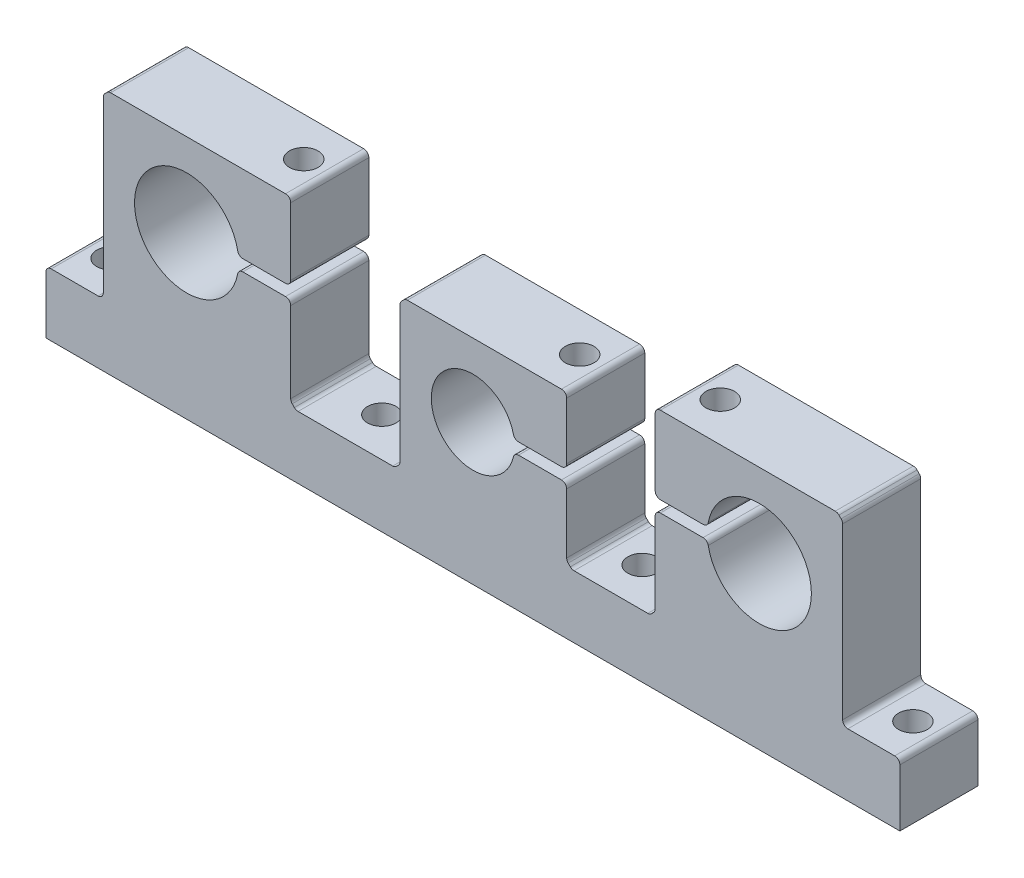
SolidWorks part; units mm, degrees
ref_plane "Front Plane" through (0, 0, 0) normal (0, 0, 1) x (1, 0, 0)
ref_plane "Top Plane" through (0, 0, 0) normal (0, 1, 0) x (1, 0, 0)
ref_plane "Right Plane" through (0, 0, 0) normal (1, 0, 0) x (0, 0, -1)
sketch "Sketch1" plane through (0, 0, 0) normal (0, 0, 1) x (1, 0, 0)
  line L0 (0, 0) -> (0, 57.1903) construction
  line L1 (82, 0) -> (-82, 0)
  line L2 (-82, 0) -> (-82, 12)
  line L3 (-82, 12) -> (-71, 12)
  line L4 (-71, 12) -> (-71, 47)
  line L5 (-71, 47) -> (71, 47)
  line L6 (82, 0) -> (82, 12)
  line L7 (82, 12) -> (71, 12)
  line L8 (71, 12) -> (71, 47)
  point P12 (0, 47)
  dimension "D1" = 82
  dimension "D2" = 12
  dimension "D3" = 47
  dimension "D4" = 71
extrude "Boss-Extrude1" add sketch "Sketch1" along normal blind 15
sketch "Sketch2" plane through (0, 0, 15) normal (0, 0, 1) x (1, 0, 0)
  line L0 (0, 0) -> (0, 27) construction
  line L1 (-82, 0) -> (82, 0) construction
  circle A0 centre (0, 27) radius 8
  dimension "D1" = 16
  dimension "D2" = 27
extrude "Cut-Extrude1" cut sketch "Sketch2" against normal up to next
sketch "Sketch3" plane through (0, 0, 0) normal (0, 0, -1) x (-1, 0, 0)
  line L0 (0, 0) -> (0, 47) construction
  line L1 (-71, 47) -> (71, 47) construction
  line L2 (-71, 31) -> (-55, 31) construction
  line L3 (-71, 12) -> (-71, 47) construction
  line L4 (82, 0) -> (-82, 0) construction
  circle A0 centre (-55, 31) radius 10
  circle A1 centre (55, 31) radius 10
  point P10 (-63, 31)
  dimension "D1" = 20
  dimension "D2" = 31
  dimension "D3" = 16
extrude "Cut-Extrude2" cut sketch "Sketch3" against normal up to next
sketch "Sketch6" plane through (0, 12, 0) normal (0, 1, 0) x (1, 0, 0)
  line L0 (-82, -7.5) -> (82, -7.5) construction
  line L1 (-82, -15) -> (-82, 0) construction
  line L2 (82, -15) -> (82, 0) construction
  line L3 (-82, -2.0107) -> (-77, -2.0107) construction
  line L4 (-77, 0) -> (-77, -9.4844) construction
  line L5 (-71, 0) -> (-82, 0) construction
  line L6 (82, -3.3711) -> (77, -3.3711) construction
  line L7 (77, -3.3711) -> (77, -12.0015) construction
  dimension "D1" = 5
  dimension "D2" = 5
hole_wizard "Ø5.5 (5.5) Diameter Hole1" positions "3DSketch3" profile "Sketch8" hole size "Ø5.5" standard "GB" end condition up to next
sketch3d "3DSketch3"
  line L0 (-82, 12, 7.5) -> (82, 12, 7.5) construction
  line L1 (-77, 12, 0) -> (-77, 12, 9.4844) construction
  line L2 (77, 12, 3.3711) -> (77, 12, 12.0015) construction
  point P0 (-77, 12, 7.5)
  point P6 (77, 12, 7.5)
sketch "Sketch8" plane through (-77, 12, 7.5) normal (1, 0, 0) x (0, 0, 1)
  line L0 (0, 0) -> (0, 12)
  line L1 (0, 12) -> (2.75, 12)
  line L2 (2.75, 12) -> (2.75, 0)
  line L5 (2.75, 0) -> (0, 0)
  line L11 (0, -6.35) -> (0, 107.95) construction
  dimension "Thru Hole Dia." = 5.5
  dimension "Thru Hole Depth" = 12
sketch "Sketch9" plane through (0, 0, 15) normal (0, 0, 1) x (1, 0, 0)
  line L0 (0, 0.821) -> (0, 56.8906) construction
  line L1 (0, 41) -> (-14, 41)
  line L2 (-14, 41) -> (-14, 12)
  line L3 (-14, 12) -> (-35, 12)
  line L4 (-35, 12) -> (-35, 47)
  line L5 (71, 47) -> (-71, 47) construction
  line L6 (0, 41) -> (18, 41)
  line L7 (18, 41) -> (18, 12)
  line L8 (18, 12) -> (35, 12)
  line L9 (35, 12) -> (35, 47)
  line L10 (-82, 0) -> (82, 0) construction
  line L11 (-55, 31) -> (-55, 50.7523) construction
  line L12 (-35, 47) -> (35, 47)
  point P19 (26.5, 12)
  dimension "D1" = 14
  dimension "D2" = 6
  dimension "D3" = 18
  dimension "D4" = 12
  dimension "D5" = 20
  dimension "D6" = 12
  dimension "D7" = 35
extrude "Cut-Extrude3" cut sketch "Sketch9" against normal up to next
sketch "Sketch10" plane through (0, 0, 15) normal (0, 0, 1) x (1, 0, 0)
  line L0 (-55, 31) -> (55, 31) construction
  line L1 (-55, 31) -> (-98.7374, 31) construction
  line L2 (55, 31) -> (79.8304, 31) construction
  line L3 (0, 27) -> (28.6792, 27) construction
  line L4 (-55, 31) -> (-55, 32.1)
  line L5 (-55, 32.1) -> (-35, 32.1)
  line L6 (-35, 47) -> (-35, 12) construction
  line L7 (-55, 31) -> (-55, 29.9)
  line L8 (-55, 29.9) -> (-35, 29.9)
  line L9 (-35, 32.1) -> (-35, 29.9)
  line L10 (55, 31) -> (55, 32.1)
  line L11 (55, 32.1) -> (35, 32.1)
  line L12 (35, 12) -> (35, 47) construction
  line L13 (55, 31) -> (55, 29.9)
  line L14 (55, 29.9) -> (35, 29.9)
  line L15 (35, 32.1) -> (35, 29.9)
  line L16 (0, 27) -> (0, 28.1)
  line L17 (0, 28.1) -> (18, 28.1)
  line L18 (18, 41) -> (18, 12) construction
  line L19 (18, 28.1) -> (18, 25.9)
  line L20 (18, 25.9) -> (0, 25.9)
  line L21 (0, 25.9) -> (0, 27)
  dimension "D1" = 1.1
  dimension "D2" = 1.1
  dimension "D3" = 1.1
  dimension "D4" = 1.1
extrude "Cut-Extrude4" cut sketch "Sketch10" against normal up to next
sketch "Sketch11" plane through (0, 47, 0) normal (0, 1, 0) x (1, 0, 0)
  line L0 (-82, -7.5) -> (82, -7.5) construction
  line L1 (-82, -15) -> (-82, 0) construction
  line L2 (82, -15) -> (82, 0) construction
  line L3 (-40, -1.2511) -> (-40, -12.3189) construction
  line L4 (-35, 0) -> (-35, -15) construction
  line L5 (40, -1.2511) -> (40, -13.334) construction
  line L6 (35, 0) -> (35, -15) construction
  line L7 (13, -2.4134) -> (13, -12.3189) construction
  line L8 (18, 0) -> (18, -15) construction
  dimension "D1" = 5
  dimension "D2" = 5
  dimension "D3" = 5
hole_wizard "Ø5.5 (5.5) Diameter Hole2" positions "3DSketch4" profile "Sketch12" hole size "Ø5.5" standard "GB" end condition up to next
sketch3d "3DSketch4"
  line L0 (-82, 47, 7.5) -> (82, 47, 7.5) construction
  line L1 (-40, 47, 1.2511) -> (-40, 47, 12.3189) construction
  line L2 (40, 47, 1.2511) -> (40, 47, 13.334) construction
  point P0 (-40, 47, 7.5)
  point P6 (40, 47, 7.5)
sketch "Sketch12" plane through (-40, 47, 7.5) normal (1, 0, 0) x (0, 0, 1)
  line L0 (0, 0) -> (0, 14.9)
  line L1 (0, 14.9) -> (2.75, 14.9)
  line L2 (2.75, 14.9) -> (2.75, 0)
  line L5 (2.75, 0) -> (0, 0)
  line L11 (0, -6.35) -> (0, 107.95) construction
  dimension "Thru Hole Dia." = 5.5
  dimension "Thru Hole Depth" = 14.9
hole_wizard "Ø5.5 (5.5) Diameter Hole3" positions "3DSketch6" profile "Sketch14" hole size "Ø5.5" standard "GB"
sketch3d "3DSketch6"
  line L0 (-82, 47, 7.5) -> (82, 47, 7.5) construction
  line L1 (13, 47, 2.4134) -> (13, 47, 12.3189) construction
  line L2 (40, 32.1, 7.5) -> (40, 47, 7.5) construction
  line L3 (-40, 32.1, 7.5) -> (-40, 47, 7.5) construction
  point P0 (13, 47, 7.5)
  point P6 (42.7784, 0, -5.3643)
  point P8 (40, 47, 7.5)
  point P12 (-40, 47, 7.5)
sketch "Sketch14" plane through (13, 47, 7.5) normal (1, 0, 0) x (0, 0, 1)
  line L0 (0, 0) -> (0, 18.9)
  line L1 (0, 18.9) -> (2.75, 18.9)
  line L2 (2.75, 18.9) -> (2.75, 0)
  line L5 (2.75, 0) -> (0, 0)
  line L11 (0, -6.35) -> (0, 107.95) construction
  dimension "Thru Hole Dia." = 5.5
  dimension "Thru Hole Depth" = 18.9
sketch "Sketch16" plane through (0, 29.9, 0) normal (0, 1, 0) x (1, 0, 0)
  line L0 (-40, -7.5) -> (40, -7.5) construction
hole_wizard "M5 Tapped Hole2" positions "3DSketch9" profile "Sketch18" tap size "M5" standard "GB"
sketch3d "3DSketch9"
  point P0 (-40, 29.9, 7.5)
  point P3 (40, 29.9, 7.5)
sketch "Sketch18" plane through (-40, 29.9, 7.5) normal (1, 0, 0) x (0, 0, 1)
  line L0 (0, 0) -> (0, 15.2618)
  line L1 (0, 15.2618) -> (2.1, 14)
  line L2 (2.1, 14) -> (2.1, 0)
  line L5 (2.1, 0) -> (0, 0)
  line L10 (0, 15.2618) -> (-2.1, 14) construction
  line L11 (0, -6.35) -> (0, 107.95) construction
  dimension "Tap Drill Dia." = 4.2
  dimension "Tap Drill Depth" = 14
  dimension "Drill Angle" = 118
cosmetic thread "Hole Thread1" parameters "D1"=10, "D2"=5
cosmetic thread "Hole Thread2" parameters "D1"=10, "D2"=5
chamfer "Chamfer1" distance 1 angle 45 2 edges at (-71, 47, 7.5) (71, 47, 7.5)
chamfer "Chamfer2" distance 1 angle 45 1 edges at (-14, 41, 7.5)
chamfer "Chamfer3" distance 1 angle 45 4 edges at (35, 12, 7.5) (18, 12, 7.5) (-14, 12, 7.5) (-35, 12, 7.5)
fillet "Fillet1" radius 1 33 edges at (82, 12, 7.5) (71, 12, 7.5) (71, 46, 7.5) (70, 47, 7.5) (45.0607, 29.9, 7.5) (45.0607, 32.1, 7.5) (35, 47, 7.5) (35, 32.1, 7.5) (35, 29.9, 7.5) (35, 13, 7.5) (34, 12, 7.5) (19, 12, 7.5) (18, 13, 7.5) (18, 25.9, 7.5) (7.924, 25.9, 7.5) (7.924, 28.1, 7.5) (18, 28.1, 7.5) (18, 41, 7.5) (-13, 41, 7.5) (-14, 40, 7.5) (-14, 13, 7.5) (-15, 12, 7.5) (-34, 12, 7.5) (-35, 13, 7.5) (-35, 29.9, 7.5) (-45.0607, 29.9, 7.5) (-45.0607, 32.1, 7.5) (-35, 32.1, 7.5) (-35, 47, 7.5) (-70, 47, 7.5) (-71, 46, 7.5) (-71, 12, 7.5) (-82, 12, 7.5)
sketch "Sketch19" plane through (0, 12, 0) normal (0, 1, 0) x (1, 0, 0)
  line L0 (0, 0) -> (0, -46.8367) construction
  line L1 (-40, -7.5) -> (85.486, -7.5) construction
  line L2 (-25, -7.5) -> (-25, -38.4714) construction
  line L3 (25, -7.5) -> (25, -37.1964) construction
  dimension "D1" = 25
  dimension "D2" = 25
hole_wizard "Ø5.5 (5.5) Diameter Hole4" positions "3DSketch10" profile "Sketch20" hole size "Ø5.5" standard "GB" end condition through all
sketch3d "3DSketch10"
  point P0 (-25, 12, 7.5)
  point P3 (25, 12, 7.5)
sketch "Sketch20" plane through (-25, 12, 7.5) normal (1, 0, 0) x (0, 0, 1)
  line L0 (0, 0) -> (0, 12)
  line L1 (0, 12) -> (2.75, 12)
  line L2 (2.75, 12) -> (2.75, 0)
  line L5 (2.75, 0) -> (0, 0)
  line L11 (0, -6.35) -> (0, 107.95) construction
  dimension "Thru Hole Dia." = 5.5
  dimension "Thru Hole Depth" = 12
